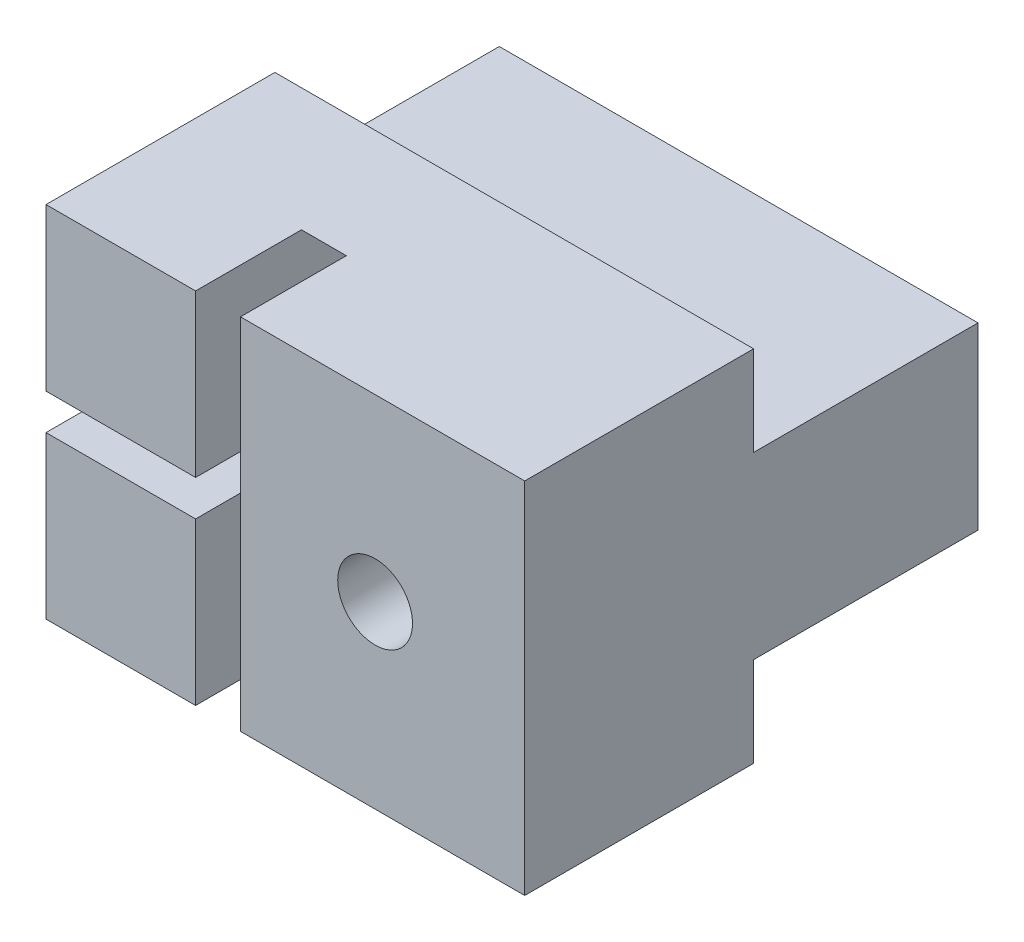
SolidWorks part; units mm, degrees
ref_plane "Спереди" through (0, 0, 0) normal (0, 0, 1) x (1, 0, 0)
ref_plane "Сверху" through (0, 0, 0) normal (0, 1, 0) x (1, 0, 0)
ref_plane "Справа" through (0, 0, 0) normal (1, 0, 0) x (0, 0, -1)
sketch "Эскиз1" plane through (0, 0, 0) normal (0, 0, 1) x (1, 0, 0)
  line L5 (-21.5997, 19) -> (-5.5997, 19)
  line L6 (-21.5997, 19) -> (-21.5997, 31)
  line L7 (-21.5997, 31) -> (-5.5997, 31)
  line L8 (-5.5997, 19) -> (-5.5997, 31)
  line L9 (-27.7383, 25) -> (-3.9171, 25) construction
  dimension "D1" = 12
  dimension "D2" = 16
extrude "Бобышка-Вытянуть1" add sketch "Эскиз1" along normal up to surface (7.65 mm away)
sketch "Эскиз2" plane through (0, 0, 7.65) normal (0, 0, 1) x (1, 0, 0)
  line L1 (-26.7383, 25) -> (-2.2483, 25) construction
  line L2 (-26.7383, 18) -> (-26.7383, 32) construction
  line L4 (-21.5997, 31) -> (-21.5997, 19) construction
  line L5 (-21.5997, 25.6) -> (-16.5997, 25.6)
  line L6 (-21.5997, 25.6) -> (-21.5997, 24.4)
  line L7 (-21.5997, 24.4) -> (-16.5997, 24.4)
  line L8 (-16.5997, 25.6) -> (-16.5997, 24.4)
  dimension "D1" = 1.2
  dimension "D2" = 5
extrude "Вырез-Вытянуть1" cut sketch "Эскиз2" against normal blind 4.5
sketch "Эскиз3" plane through (-16.5997, 0, 0) normal (-1, 0, 0) x (0, 0, 1)
  circle A0 centre (8, 25) radius 7.15
  dimension "D1" = 14.3
extrude "Вырез-Вытянуть2" cut sketch "Эскиз3" against normal blind 1.5
sketch "Эскиз4" plane through (0, 0, 0) normal (0, 0, -1) x (-1, 0, 0)
  line L0 (5.5997, 19) -> (5.5997, 31) construction
  line L1 (5.5997, 28) -> (21.5997, 28)
  line L2 (5.5997, 28) -> (5.5997, 22)
  line L3 (5.5997, 22) -> (21.5997, 22)
  line L4 (21.5997, 28) -> (21.5997, 22)
  line L5 (21.5997, 31) -> (21.5997, 19) construction
  line L6 (5.5997, 31) -> (21.5997, 31) construction
  dimension "D1" = 6
  dimension "D2" = 3
extrude "Бобышка-Вытянуть2" add sketch "Эскиз4" along normal blind 7.5
sketch "Эскиз5" plane through (0, 0, -7.5) normal (0, 0, -1) x (-1, 0, 0)
  line L0 (5.5997, 28) -> (5.5997, 22) construction
  line L2 (21.5997, 19) -> (5.5997, 19) construction
  circle A0 centre (10.5997, 25) radius 2.25
  dimension "D1" = 4.5
  dimension "D2" = 5
  dimension "D3" = 6
extrude "Вырез-Вытянуть3" cut sketch "Эскиз5" against normal up to surface (7.5 mm away) up to face at (-13.5997, 29.5, 0)
sketch "Эскиз6" plane through (0, 0, 0) normal (0, 0, -1) x (-1, 0, 0)
  circle A0 centre (10.5997, 25) radius 1.25
  dimension "D1" = 2.5
extrude "Вырез-Вытянуть4" cut sketch "Эскиз6" against normal through all
